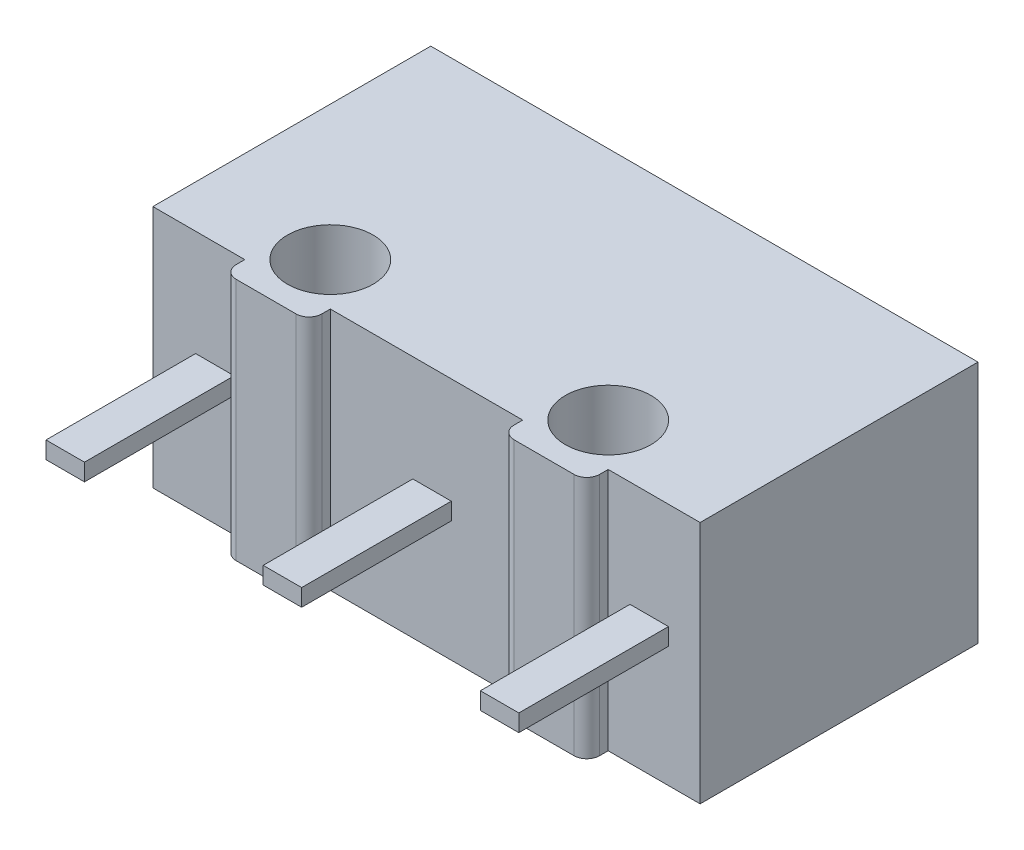
SolidWorks part; units mm, degrees
ref_plane "Front Plane" through (0, 0, 0) normal (0, 0, 1) x (1, 0, 0)
ref_plane "Top Plane" through (0, 0, 0) normal (0, 1, 0) x (1, 0, 0)
ref_plane "Right Plane" through (0, 0, 0) normal (1, 0, 0) x (0, 0, -1)
sketch "Sketch1" plane through (0, 0, 0) normal (0, 1, 0) x (1, 0, 0)
  line L0 (0, 0) -> (2.15, 0)
  line L1 (2.15, 0) -> (2.15, -0.2)
  line L2 (0, 0) -> (0, 6.5)
  line L3 (0, 6.5) -> (12.8, 6.5)
  line L4 (12.8, 0) -> (12.8, 6.5)
  line L5 (2.45, -0.5) -> (3.85, -0.5)
  line L6 (4.15, -0.2) -> (4.15, 0)
  line L7 (4.15, 0) -> (8.65, 0)
  line L8 (8.65, 0) -> (8.65, -0.2)
  line L9 (8.95, -0.5) -> (10.35, -0.5)
  line L10 (10.65, -0.2) -> (10.65, 0)
  line L11 (10.65, 0) -> (12.8, 0)
  circle A0 centre (3.15, 1) radius 1
  circle A1 centre (9.65, 1) radius 1
  arc A2 (10.35, -0.5) -> (10.65, -0.2) centre (10.35, -0.2) ccw
  arc A3 (8.65, -0.2) -> (8.95, -0.5) centre (8.95, -0.2) ccw
  arc A4 (3.85, -0.5) -> (4.15, -0.2) centre (3.85, -0.2) ccw
  arc A5 (2.15, -0.2) -> (2.45, -0.5) centre (2.45, -0.2) ccw
  dimension "D1" = 3.15
  dimension "D2" = 0.3
  dimension "D3" = 6.5
  dimension "D4" = 12.8
  dimension "D5" = 6.5
extrude "Boss-Extrude1" add sketch "Sketch1" along normal blind 5.7
sketch "Sketch2" plane through (0, 0, -6.5) normal (0, 0, -1) x (-1, 0, 0)
  line L0 (-12.8, 5.7) -> (0, 5.7) construction
  line L1 (-8.95, 4.25) -> (-7.75, 4.25)
  line L2 (-8.95, 4.25) -> (-8.95, 1.35)
  line L3 (-8.95, 1.35) -> (-7.75, 1.35)
  line L4 (-7.75, 4.25) -> (-7.75, 1.35)
  line L5 (0, 5.7) -> (0, 0) construction
  dimension "D1" = 1.2
  dimension "D2" = 2.9
  dimension "D3" = 1.45
  dimension "D4" = 7.75
extrude "Boss-Extrude2" add sketch "Sketch2" along normal blind 0.85
fillet "Fillet1" radius 0.5 2 edges at (7.75, 2.8, -7.35) (8.95, 2.8, -7.35)
sketch "Sketch3" plane through (0, 0, 0) normal (0, 0, 1) x (1, 0, 0)
  line L0 (0, 5.7) -> (0, 0) construction
  line L1 (1, 3.2221) -> (1.9, 3.2221)
  line L2 (1, 3.2221) -> (1, 2.8221)
  line L3 (1, 2.8221) -> (1.9, 2.8221)
  line L4 (1.9, 3.2221) -> (1.9, 2.8221)
  line L5 (6.08, 3.2221) -> (6.98, 3.2221)
  line L6 (6.08, 3.2221) -> (6.08, 2.8221)
  line L7 (6.08, 2.8221) -> (6.98, 2.8221)
  line L8 (6.98, 3.2221) -> (6.98, 2.8221)
  line L9 (11.16, 3.2221) -> (12.06, 3.2221)
  line L10 (11.16, 3.2221) -> (11.16, 2.8221)
  line L11 (11.16, 2.8221) -> (12.06, 2.8221)
  line L12 (12.06, 3.2221) -> (12.06, 2.8221)
  dimension "D1" = 0.9
  dimension "D2" = 0.4
  dimension "D3" = 1
  dimension "D4" = 3
extrude "Boss-Extrude3" add sketch "Sketch3" along normal blind 3.5
